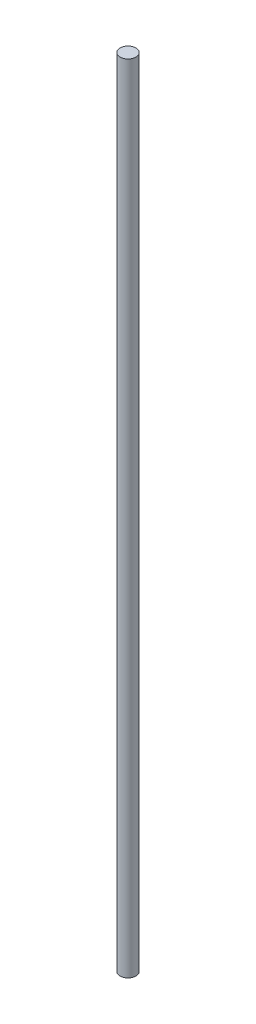
SolidWorks part; units mm, degrees
ref_plane "Front Plane" through (0, 0, 0) normal (0, 0, 1) x (1, 0, 0)
ref_plane "Top Plane" through (0, 0, 0) normal (0, 1, 0) x (1, 0, 0)
ref_plane "Right Plane" through (0, 0, 0) normal (1, 0, 0) x (0, 0, -1)
sketch "Sketch1" plane through (0, 0, 0) normal (0, 1, 0) x (1, 0, 0)
  circle A0 centre (0, 0) radius 2
  dimension "D1" = 4
extrude "Boss-Extrude1" add sketch "Sketch1" along normal blind 200
